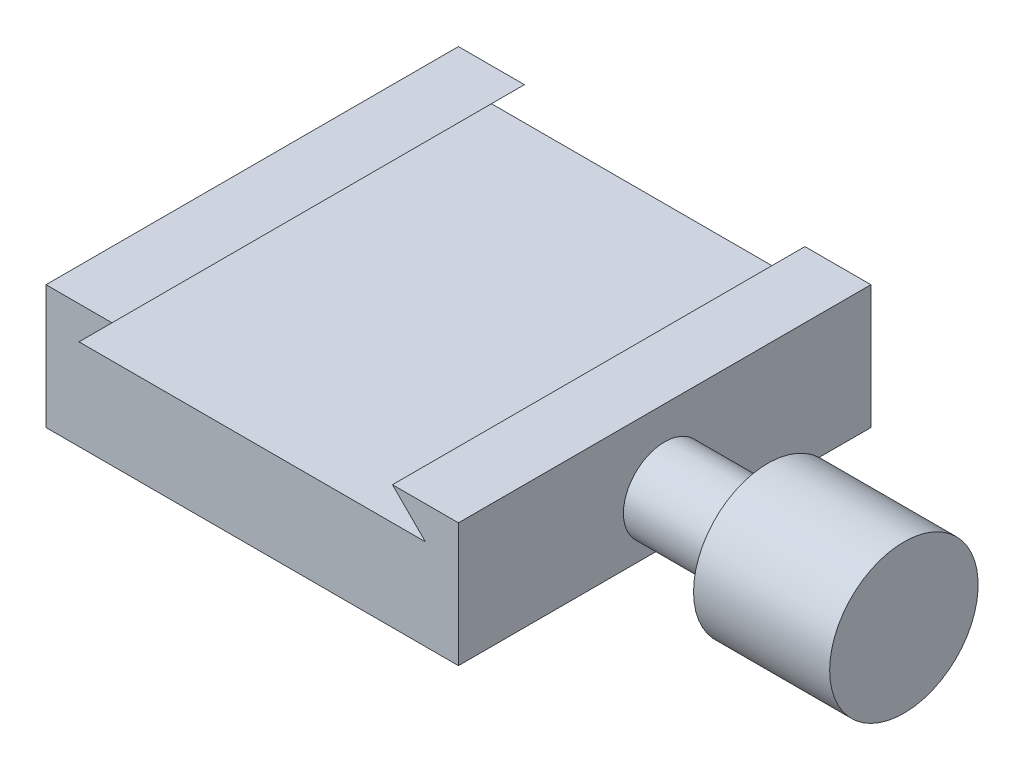
SolidWorks part; units mm, degrees
ref_plane "Front Plane" through (0, 0, 0) normal (0, 0, 1) x (1, 0, 0)
ref_plane "Top Plane" through (0, 0, 0) normal (0, 1, 0) x (1, 0, 0)
ref_plane "Right Plane" through (0, 0, 0) normal (1, 0, 0) x (0, 0, -1)
sketch "Sketch1" plane through (0, 0, 0) normal (0, 0, 1) x (1, 0, 0)
  line L0 (0, 0) -> (0, 15)
  line L1 (0, 15) -> (8, 15)
  line L2 (8, 15) -> (4, 11)
  line L3 (4, 11) -> (46, 11)
  line L4 (46, 11) -> (42, 15)
  line L5 (42, 15) -> (50, 15)
  line L6 (50, 15) -> (50, 0)
  line L7 (50, 0) -> (0, 0)
  point P3 (25, 11)
  point P10 (25, 0)
  point P11 (42, 20.4384)
  dimension "D1" = 50
  dimension "D2" = 15
  dimension "D3" = 4
  dimension "D4" = 8
  dimension "D5" = 4
extrude "Boss-Extrude1" add sketch "Sketch1" along normal blind 50
ref_plane "Plane1" through (0, 0, 25) normal (0, 0, 1) x (1, 0, 0)
sketch "Sketch2" plane through (0, 0, 25) normal (0, 0, 1) x (1, 0, 0)
  line L0 (50, 6) -> (50, 1)
  line L1 (50, 1) -> (62.5, 1)
  line L2 (62.5, 1) -> (62.5, -3)
  line L3 (62.5, -3) -> (79, -3)
  line L4 (79, -3) -> (79, 6)
  line L9 (50, 0) -> (50, 15) construction
  line L10 (0, 0) -> (50, 0) construction
  line L11 (50, 6) -> (79, 6)
  point P0 (62.5, -2.5458)
  dimension "D1" = 12.5
  dimension "D2" = 29
  dimension "D3" = 5
  dimension "D4" = 9
  dimension "D5" = 1
revolve "Revolve2" add sketch "Sketch2" angle 360 about L11
sketch "Sketch3" plane through (0, 0, 0) normal (0, -1, 0) x (1, 0, 0)
  line L0 (0, 0) -> (50, 0) construction
  line L1 (0, 50) -> (0, 0) construction
  circle A0 centre (25, 25) radius 4.7625
  point P4 (25, 0)
  point P7 (0, 25)
  dimension "D1" = 9.525
extrude "Cut-Extrude1" cut sketch "Sketch3" against normal blind 6.35
